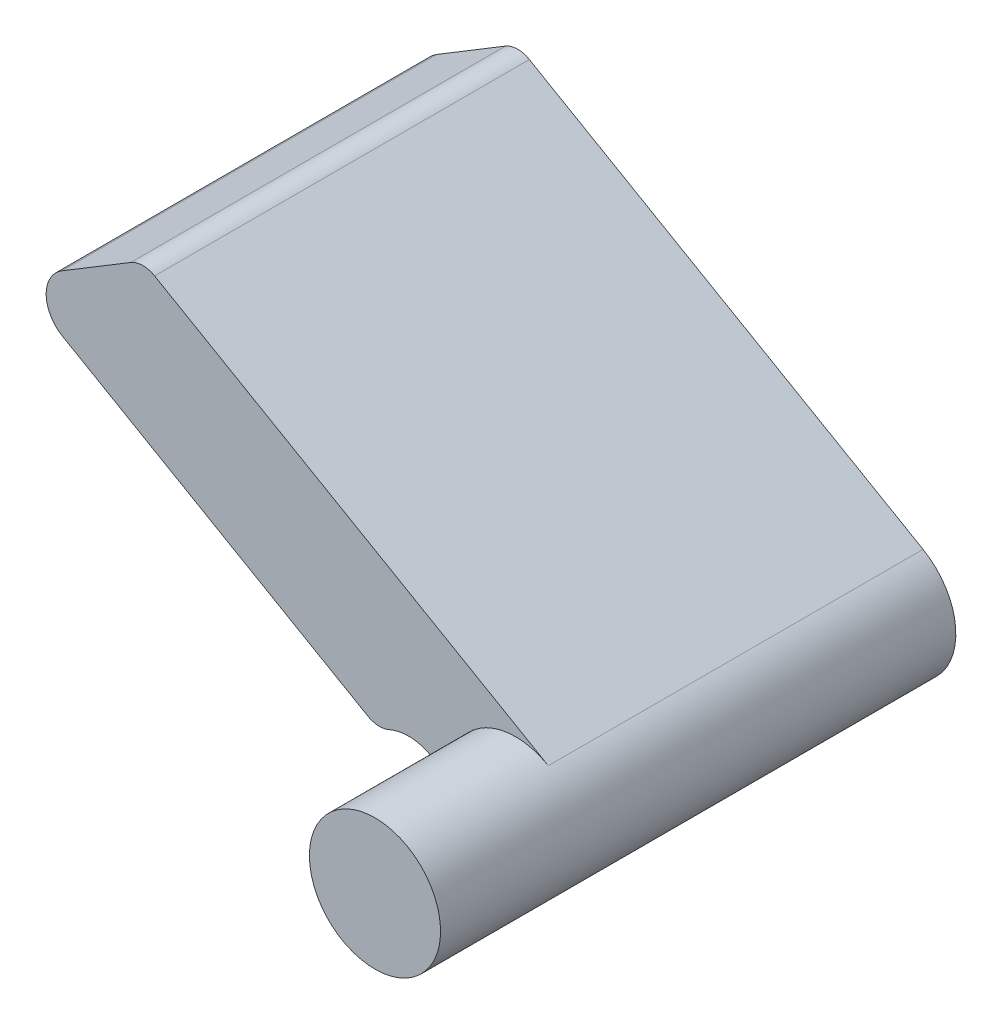
SolidWorks part; units mm, degrees
ref_plane "前视基准面" through (0, 0, 0) normal (0, 0, 1) x (1, 0, 0)
ref_plane "上视基准面" through (0, 0, 0) normal (0, 1, 0) x (1, 0, 0)
ref_plane "右视基准面" through (0, 0, 0) normal (1, 0, 0) x (0, 0, -1)
sketch "草图1" plane through (0, 0, 0) normal (0, 0, 1) x (1, 0, 0)
  line L0 (0.7, 1.2124) -> (-7.9603, 6.2124)
  line L1 (-7.9603, 6.2124) -> (-10.6942, 4.5577)
  line L2 (-10.6942, 4.5577) -> (-2.9, 0.0577)
  line L3 (0.7, 1.2124) -> (-5.1246, 1.2124) construction
  line L4 (0, 0) -> (0, 5.0845) construction
  line L5 (0, 0) -> (3.6976, 0) construction
  arc A0 (-1.3334, -0.4267) -> (0.7, 1.2124) centre (0, 0) ccw
  arc A1 (-2.9, 0.0577) -> (-1.3334, -0.4267) centre (-2.2858, -0.7314) cw
  dimension "D1" = 1
  dimension "D5" = 1.4
  dimension "D2" = 10
  dimension "D3" = 9
  dimension "D4" = 30
  dimension "D6" = 2.9
extrude "凸台-拉伸1" add sketch "草图1" along normal blind 8 contours L2 A1 A0 L0 L1
fillet "圆角1" radius 0.5 2 edges at (-7.9603, 6.2124, 4) (-2.9, 0.0577, 4)
fillet "圆角2" radius 0.7 1 edges at (-10.6942, 4.5577, 4)
sketch "草图2" plane through (0, 0, 0) normal (0, 0, -1) x (-1, 0, 0)
  circle A0 centre (0, 0) radius 1.4
  dimension "D1" = 2.8
extrude "凸台-拉伸2" add sketch "草图2" against normal blind 3 from surface at -8 starting at face at (-5.0957, 2.6579, 8)
